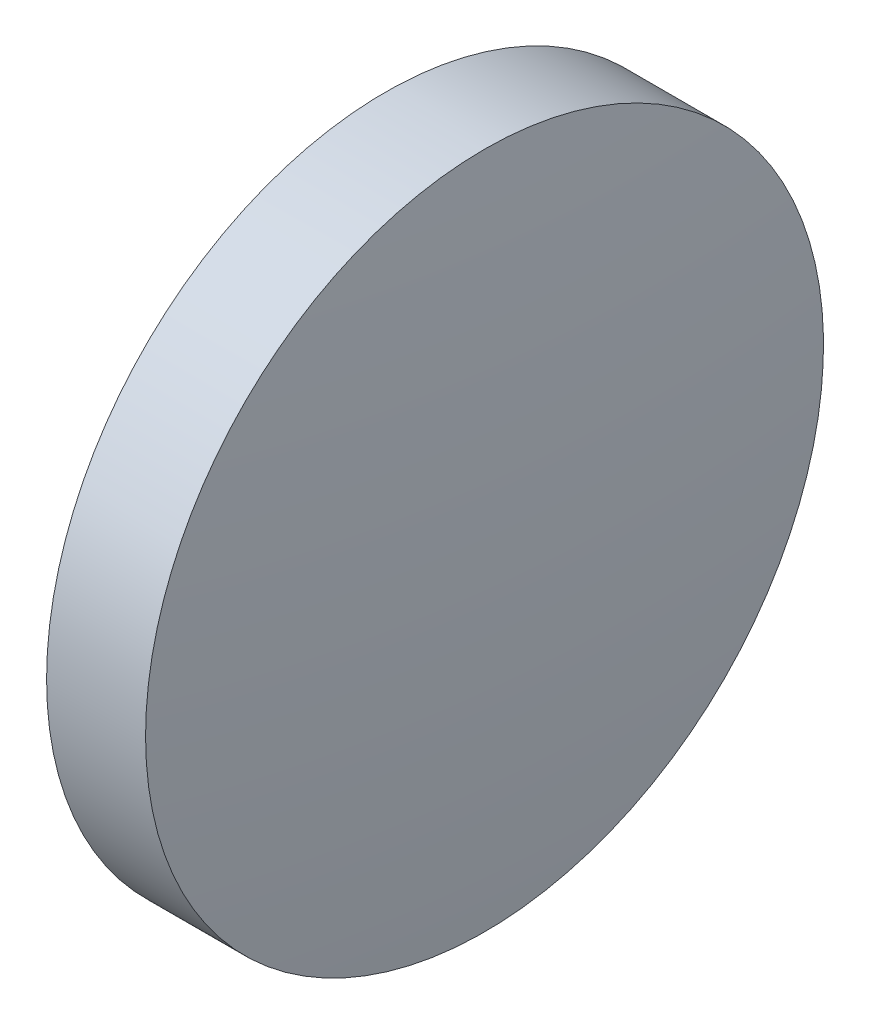
SolidWorks part; units mm, degrees
ref_plane "前视基准面" through (0, 0, 0) normal (0, 0, 1) x (1, 0, 0)
ref_plane "上视基准面" through (0, 0, 0) normal (0, 1, 0) x (1, 0, 0)
ref_plane "右视基准面" through (0, 0, 0) normal (1, 0, 0) x (0, 0, -1)
sketch "草图1" plane through (0, 0, 0) normal (0, 0, 1) x (1, 0, 0)
  line L0 (421.984, 168.3693) -> (428.1194, 168.3693) construction
  line L1 (422.9255, 168.3693) -> (422.9255, 173.3693)
  line L2 (424.6255, 168.3693) -> (422.9255, 168.3693)
  line L5 (422.9255, 173.3693) -> (424.3855, 173.3693)
  arc A0 (424.6255, 168.3693) -> (424.3855, 173.3693) centre (372.4222, 168.3693) ccw
revolve "旋转1" add sketch "草图1" angle 360 about L0
